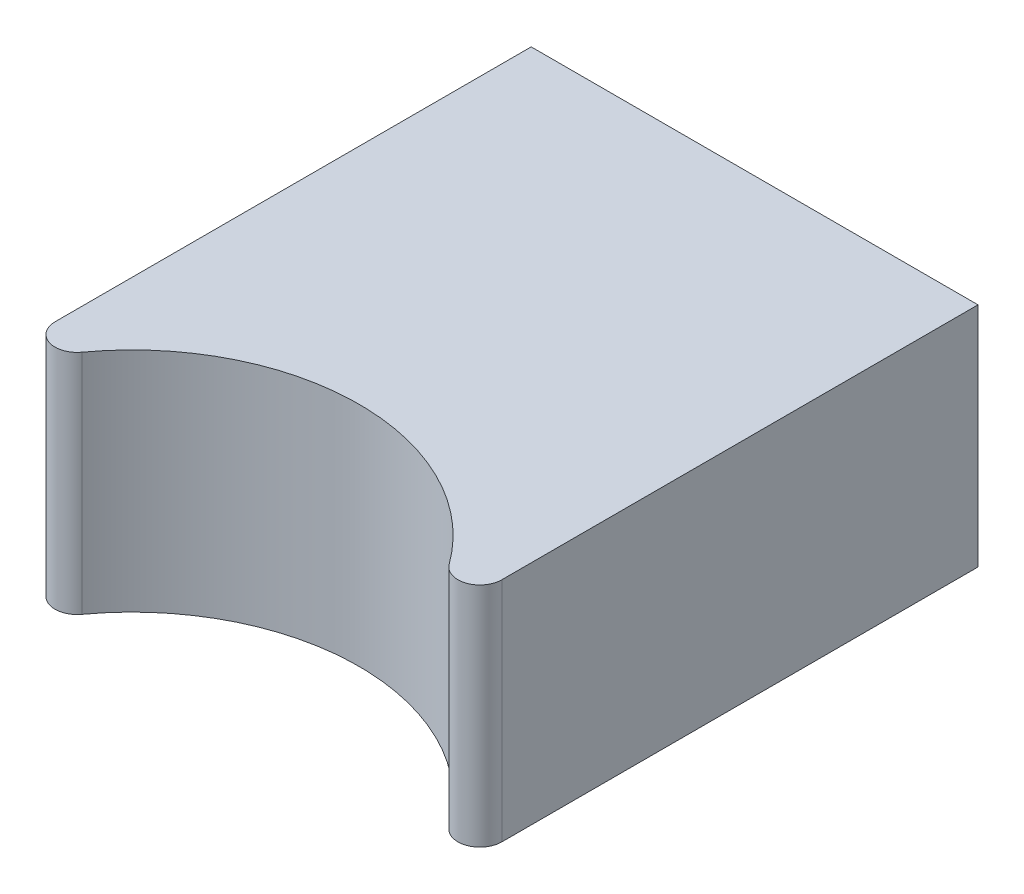
SolidWorks part; units mm, degrees
ref_plane "Front Plane" through (0, 0, 0) normal (0, 0, 1) x (1, 0, 0)
ref_plane "Top Plane" through (0, 0, 0) normal (0, 1, 0) x (1, 0, 0)
ref_plane "Right Plane" through (0, 0, 0) normal (1, 0, 0) x (0, 0, -1)
sketch "Sketch1" plane through (0, 0, 0) normal (0, 1, 0) x (1, 0, 0)
  line L0 (-3.05, -2.7) -> (-3.05, -5.2455)
  line L1 (-3.05, -2.7) -> (3.05, -2.7)
  line L2 (-3.05, -2.7) -> (-3.05, 2.7)
  line L3 (-3.05, 2.7) -> (3.05, 2.7)
  line L4 (3.05, -2.7) -> (3.05, 2.7)
  line L5 (-3.05, -2.7) -> (3.05, 2.7) construction
  line L6 (-3.05, 2.7) -> (3.05, -2.7) construction
  line L7 (3.05, -2.7) -> (3.05, -5.2455)
  circle A0 centre (0, -5.8) radius 3.1
  point P0 (0, 0)
  point P8 (0, 0)
  point P11 (-3.05, -5.2455)
  dimension "D3" = 6.2
  dimension "D1" = 6.1
  dimension "D2" = 5.4
extrude "Boss-Extrude2" add sketch "Sketch1" along normal blind 3.1 contours L1 L4 L3 L2 | A0 L1 L0 | A0 L7 L1
fillet "Fillet1" radius 0.3 2 edges at (3.05, 1.55, 5.2455) (-3.05, 1.55, 5.2455)
